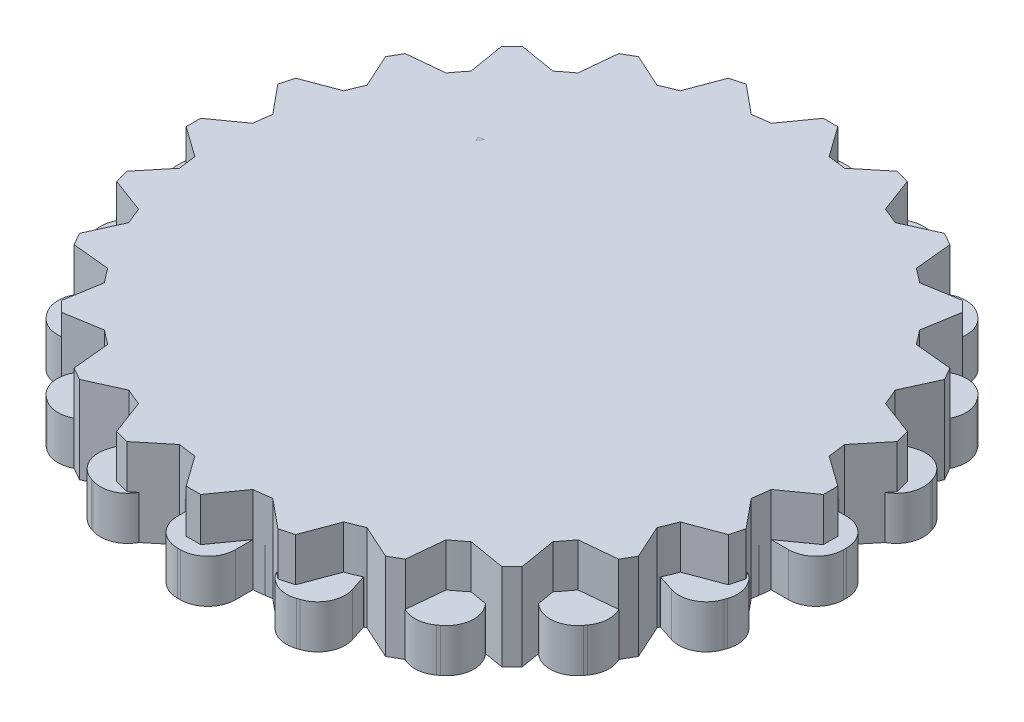
SolidWorks part; units mm, degrees
ref_plane "Front Plane" through (0, 0, 0) normal (0, 0, 1) x (1, 0, 0)
ref_plane "Top Plane" through (0, 0, 0) normal (0, 1, 0) x (1, 0, 0)
ref_plane "Right Plane" through (0, 0, 0) normal (1, 0, 0) x (0, 0, -1)
sketch "Sketch1" plane through (0, 0, 0) normal (0, 1, 0) x (1, 0, 0)
  line L86 (-3.1424, 4.8669) -> (1.8576, 4.8669)
  line L87 (-3.1424, 4.8669) -> (-3.1424, 1.8669)
  line L111 (-1.1424, 15.3669) -> (-0.1424, 15.3669)
  line L112 (-0.1424, 15.3669) -> (1.3576, 13.1649)
  line L113 (-1.1424, 15.3669) -> (-2.6424, 13.1649)
  line L114 (5.7906, 13.5092) -> (5.9886, 10.8522)
  line L115 (4.9246, 14.0092) -> (5.7906, 13.5092)
  line L116 (4.9246, 14.0092) -> (2.5245, 12.8522)
  line L117 (9.9999, 8.9339) -> (8.8429, 6.5338)
  line L118 (9.4999, 9.7999) -> (9.9999, 8.9339)
  line L119 (9.4999, 9.7999) -> (6.8429, 9.9979)
  line L120 (11.3576, 2.8669) -> (9.1556, 1.3669)
  line L121 (11.3576, 3.8669) -> (11.3576, 2.8669)
  line L122 (11.3576, 3.8669) -> (9.1556, 5.3669)
  line L123 (9.4999, -3.0661) -> (6.8429, -3.2641)
  line L124 (9.9999, -2.2001) -> (9.4999, -3.0661)
  line L125 (9.9999, -2.2001) -> (8.8429, 0.2)
  line L126 (4.9246, -7.2754) -> (2.5245, -6.1184)
  line L127 (5.7906, -6.7754) -> (4.9246, -7.2754)
  line L128 (5.7906, -6.7754) -> (5.9886, -4.1184)
  line L129 (-1.1424, -8.6331) -> (-2.6424, -6.4311)
  line L130 (-0.1424, -8.6331) -> (-1.1424, -8.6331)
  line L131 (-0.1424, -8.6331) -> (1.3576, -6.4311)
  line L132 (-7.0754, -6.7754) -> (-7.2734, -4.1184)
  line L133 (-6.2094, -7.2754) -> (-7.0754, -6.7754)
  line L134 (-6.2094, -7.2754) -> (-3.8093, -6.1184)
  line L135 (-11.2847, -2.2001) -> (-10.1277, 0.2)
  line L136 (-10.7847, -3.0661) -> (-11.2847, -2.2001)
  line L137 (-10.7847, -3.0661) -> (-8.1277, -3.2641)
  line L138 (-12.6424, 3.8669) -> (-10.4404, 5.3669)
  line L139 (-12.6424, 2.8669) -> (-12.6424, 3.8669)
  line L140 (-12.6424, 2.8669) -> (-10.4404, 1.3669)
  line L141 (-10.7847, 9.7999) -> (-8.1277, 9.9979)
  line L142 (-11.2847, 8.9339) -> (-10.7847, 9.7999)
  line L143 (-11.2847, 8.9339) -> (-10.1277, 6.5338)
  line L144 (-6.2094, 14.0092) -> (-3.8093, 12.8522)
  line L145 (-7.0754, 13.5092) -> (-6.2094, 14.0092)
  line L146 (-7.0754, 13.5092) -> (-7.2734, 10.8522)
  line L147 (-3.1424, 1.8669) -> (1.8576, 1.8669)
  line L148 (1.8576, 4.8669) -> (1.8576, 1.8669)
  line L149 (-3.1424, 4.8669) -> (1.8576, 1.8669) construction
  line L150 (-3.1424, 1.8669) -> (1.8576, 4.8669) construction
  arc A43 (-2.6424, 13.1649) -> (-3.8093, 12.8522) centre (-0.6424, 3.3669) ccw
  arc A44 (-7.2734, 10.8522) -> (-8.1277, 9.9979) centre (-0.6424, 3.3669) ccw
  arc A45 (-10.1277, 6.5338) -> (-10.4404, 5.3669) centre (-0.6424, 3.3669) ccw
  arc A46 (-10.4404, 1.3669) -> (-10.1277, 0.2) centre (-0.6424, 3.3669) ccw
  arc A47 (-8.1277, -3.2641) -> (-7.2734, -4.1184) centre (-0.6424, 3.3669) ccw
  arc A48 (-3.8093, -6.1184) -> (-2.6424, -6.4311) centre (-0.6424, 3.3669) ccw
  arc A49 (1.3576, -6.4311) -> (2.5245, -6.1184) centre (-0.6424, 3.3669) ccw
  arc A50 (5.9886, -4.1184) -> (6.8429, -3.2641) centre (-0.6424, 3.3669) ccw
  arc A51 (8.8429, 0.2) -> (9.1556, 1.3669) centre (-0.6424, 3.3669) ccw
  arc A52 (9.1556, 5.3669) -> (8.8429, 6.5338) centre (-0.6424, 3.3669) ccw
  arc A53 (6.8429, 9.9979) -> (5.9886, 10.8522) centre (-0.6424, 3.3669) ccw
  arc A54 (2.5245, 12.8522) -> (1.3576, 13.1649) centre (-0.6424, 3.3669) ccw
  point P6 (0, 0)
  point P8 (0, 0)
  point P9 (0, 0)
  point P12 (0, 2.7462)
  point P17 (0, 0)
  point P18 (0, 2.7462)
  point P22 (-2.5, 0.7462)
  point P63 (0, 0)
  point P68 (0, 0)
  point P69 (-0.6424, 3.3669)
  point P119 (0, 0)
  dimension "D1" = 20
  dimension "D2" = 3
  dimension "D3" = 5
  dimension "D8" = 12
sketch "Sketch2" plane through (0, 0, 0) normal (0, 1, 0) x (1, 0, 0)
  line L0 (-2, 0) -> (2, 0)
  line L1 (-23, -0.1) -> (-23, 0.1)
  line L2 (-21.1, 2) -> (-19.8997, 2)
  line L3 (-21.1, -2) -> (-19.8997, -2)
  line L4 (-20.6853, 4.6181) -> (-19.5438, 4.2472)
  line L5 (-19.4493, 8.4224) -> (-18.3078, 8.0515)
  line L6 (-21.9052, 7.0123) -> (-21.8434, 7.2025)
  line L7 (-18.2458, 10.7842) -> (-17.2748, 10.0787)
  line L8 (-15.8947, 14.0203) -> (-14.9237, 13.3148)
  line L9 (-18.6662, 13.4382) -> (-18.5486, 13.6)
  line L10 (-14.0203, 15.8947) -> (-13.3148, 14.9237)
  line L11 (-10.7842, 18.2458) -> (-10.0787, 17.2748)
  line L12 (-13.6, 18.5486) -> (-13.4382, 18.6662)
  line L13 (-8.4224, 19.4493) -> (-8.0515, 18.3078)
  line L14 (-4.6181, 20.6853) -> (-4.2472, 19.5438)
  line L15 (-7.2025, 21.8434) -> (-7.0123, 21.9052)
  line L16 (-2, 21.1) -> (-2, 19.8997)
  line L17 (2, 21.1) -> (2, 19.8997)
  line L18 (-0.1, 23) -> (0.1, 23)
  line L19 (4.6181, 20.6853) -> (4.2472, 19.5438)
  line L20 (8.4224, 19.4493) -> (8.0515, 18.3078)
  line L21 (7.0123, 21.9052) -> (7.2025, 21.8434)
  line L22 (10.7842, 18.2458) -> (10.0787, 17.2748)
  line L23 (14.0203, 15.8947) -> (13.3148, 14.9237)
  line L24 (13.4382, 18.6662) -> (13.6, 18.5486)
  line L25 (15.8947, 14.0203) -> (14.9237, 13.3148)
  line L26 (18.2458, 10.7842) -> (17.2748, 10.0787)
  line L27 (18.5486, 13.6) -> (18.6662, 13.4382)
  line L28 (19.4493, 8.4224) -> (18.3078, 8.0515)
  line L29 (20.6853, 4.6181) -> (19.5438, 4.2472)
  line L30 (21.8434, 7.2025) -> (21.9052, 7.0123)
  line L31 (21.1, 2) -> (19.8997, 2)
  line L32 (21.1, -2) -> (19.8997, -2)
  line L33 (23, 0.1) -> (23, -0.1)
  line L34 (20.6853, -4.6181) -> (19.5438, -4.2472)
  line L35 (19.4493, -8.4224) -> (18.3078, -8.0515)
  line L36 (21.9052, -7.0123) -> (21.8434, -7.2025)
  line L37 (18.2458, -10.7842) -> (17.2748, -10.0787)
  line L38 (15.8947, -14.0203) -> (14.9237, -13.3148)
  line L39 (18.6662, -13.4382) -> (18.5486, -13.6)
  line L40 (14.0203, -15.8947) -> (13.3148, -14.9237)
  line L41 (10.7842, -18.2458) -> (10.0787, -17.2748)
  line L42 (13.6, -18.5486) -> (13.4382, -18.6662)
  line L43 (8.4224, -19.4493) -> (8.0515, -18.3078)
  line L44 (4.6181, -20.6853) -> (4.2472, -19.5438)
  line L45 (7.2025, -21.8434) -> (7.0123, -21.9052)
  line L46 (2, -21.1) -> (2, -19.8997)
  line L47 (-2, -21.1) -> (-2, -19.8997)
  line L48 (0.1, -23) -> (-0.1, -23)
  line L49 (-4.6181, -20.6853) -> (-4.2472, -19.5438)
  line L50 (-8.4224, -19.4493) -> (-8.0515, -18.3078)
  line L51 (-7.0123, -21.9052) -> (-7.2025, -21.8434)
  line L52 (-10.7842, -18.2458) -> (-10.0787, -17.2748)
  line L53 (-14.0203, -15.8947) -> (-13.3148, -14.9237)
  line L54 (-13.4382, -18.6662) -> (-13.6, -18.5486)
  line L55 (-15.8947, -14.0203) -> (-14.9237, -13.3148)
  line L56 (-18.2458, -10.7842) -> (-17.2748, -10.0787)
  line L57 (-18.5486, -13.6) -> (-18.6662, -13.4382)
  line L58 (-19.4493, -8.4224) -> (-18.3078, -8.0515)
  line L59 (-20.6853, -4.6181) -> (-19.5438, -4.2472)
  line L60 (-21.8434, -7.2025) -> (-21.9052, -7.0123)
  arc A0 (-18.3078, -8.0515) -> (-17.2748, -10.0787) centre (0, 0) ccw
  arc A1 (-21.1, 2) -> (-23, 0.1) centre (-21.1, 0.1) ccw
  arc A2 (-21.1, -2) -> (-23, -0.1) centre (-21.1, -0.1) cw
  arc A3 (-20.6853, 4.6181) -> (-21.9052, 7.0123) centre (-20.0982, 6.4252) cw
  arc A4 (-19.4493, 8.4224) -> (-21.8434, 7.2025) centre (-20.0364, 6.6154) ccw
  arc A5 (-18.2458, 10.7842) -> (-18.6662, 13.4382) centre (-17.129, 12.3214) cw
  arc A6 (-15.8947, 14.0203) -> (-18.5486, 13.6) centre (-17.0115, 12.4832) ccw
  arc A7 (-14.0203, 15.8947) -> (-13.6, 18.5486) centre (-12.4832, 17.0115) cw
  arc A8 (-10.7842, 18.2458) -> (-13.4382, 18.6662) centre (-12.3214, 17.129) ccw
  arc A9 (-8.4224, 19.4493) -> (-7.2025, 21.8434) centre (-6.6154, 20.0364) cw
  arc A10 (-4.6181, 20.6853) -> (-7.0123, 21.9052) centre (-6.4252, 20.0982) ccw
  arc A11 (-2, 21.1) -> (-0.1, 23) centre (-0.1, 21.1) cw
  arc A12 (2, 21.1) -> (0.1, 23) centre (0.1, 21.1) ccw
  arc A13 (4.6181, 20.6853) -> (7.0123, 21.9052) centre (6.4252, 20.0982) cw
  arc A14 (8.4224, 19.4493) -> (7.2025, 21.8434) centre (6.6154, 20.0364) ccw
  arc A15 (10.7842, 18.2458) -> (13.4382, 18.6662) centre (12.3214, 17.129) cw
  arc A16 (14.0203, 15.8947) -> (13.6, 18.5486) centre (12.4832, 17.0115) ccw
  arc A17 (15.8947, 14.0203) -> (18.5486, 13.6) centre (17.0115, 12.4832) cw
  arc A18 (18.2458, 10.7842) -> (18.6662, 13.4382) centre (17.129, 12.3214) ccw
  arc A19 (19.4493, 8.4224) -> (21.8434, 7.2025) centre (20.0364, 6.6154) cw
  arc A20 (20.6853, 4.6181) -> (21.9052, 7.0123) centre (20.0982, 6.4252) ccw
  arc A21 (21.1, 2) -> (23, 0.1) centre (21.1, 0.1) cw
  arc A22 (21.1, -2) -> (23, -0.1) centre (21.1, -0.1) ccw
  arc A23 (20.6853, -4.6181) -> (21.9052, -7.0123) centre (20.0982, -6.4252) cw
  arc A24 (19.4493, -8.4224) -> (21.8434, -7.2025) centre (20.0364, -6.6154) ccw
  arc A25 (18.2458, -10.7842) -> (18.6662, -13.4382) centre (17.129, -12.3214) cw
  arc A26 (15.8947, -14.0203) -> (18.5486, -13.6) centre (17.0115, -12.4832) ccw
  arc A27 (14.0203, -15.8947) -> (13.6, -18.5486) centre (12.4832, -17.0115) cw
  arc A28 (10.7842, -18.2458) -> (13.4382, -18.6662) centre (12.3214, -17.129) ccw
  arc A29 (8.4224, -19.4493) -> (7.2025, -21.8434) centre (6.6154, -20.0364) cw
  arc A30 (4.6181, -20.6853) -> (7.0123, -21.9052) centre (6.4252, -20.0982) ccw
  arc A31 (2, -21.1) -> (0.1, -23) centre (0.1, -21.1) cw
  arc A32 (-2, -21.1) -> (-0.1, -23) centre (-0.1, -21.1) ccw
  arc A33 (-4.6181, -20.6853) -> (-7.0123, -21.9052) centre (-6.4252, -20.0982) cw
  arc A34 (-8.4224, -19.4493) -> (-7.2025, -21.8434) centre (-6.6154, -20.0364) ccw
  arc A35 (-10.7842, -18.2458) -> (-13.4382, -18.6662) centre (-12.3214, -17.129) cw
  arc A36 (-14.0203, -15.8947) -> (-13.6, -18.5486) centre (-12.4832, -17.0115) ccw
  arc A37 (-15.8947, -14.0203) -> (-18.5486, -13.6) centre (-17.0115, -12.4832) cw
  arc A38 (-18.2458, -10.7842) -> (-18.6662, -13.4382) centre (-17.129, -12.3214) ccw
  arc A39 (-19.4493, -8.4224) -> (-21.8434, -7.2025) centre (-20.0364, -6.6154) cw
  arc A40 (-20.6853, -4.6181) -> (-21.9052, -7.0123) centre (-20.0982, -6.4252) ccw
  arc A41 (-19.8997, -2) -> (-19.5438, -4.2472) centre (0, 0) ccw
  arc A42 (-19.5438, 4.2472) -> (-19.8997, 2) centre (0, 0) ccw
  arc A43 (-17.2748, 10.0787) -> (-18.3078, 8.0515) centre (0, 0) ccw
  arc A44 (-13.3148, 14.9237) -> (-14.9237, 13.3148) centre (0, 0) ccw
  arc A45 (-8.0515, 18.3078) -> (-10.0787, 17.2748) centre (0, 0) ccw
  arc A46 (-2, 19.8997) -> (-4.2472, 19.5438) centre (0, 0) ccw
  arc A47 (4.2472, 19.5438) -> (2, 19.8997) centre (0, 0) ccw
  arc A48 (10.0787, 17.2748) -> (8.0515, 18.3078) centre (0, 0) ccw
  arc A49 (14.9237, 13.3148) -> (13.3148, 14.9237) centre (0, 0) ccw
  arc A50 (18.3078, 8.0515) -> (17.2748, 10.0787) centre (0, 0) ccw
  arc A51 (19.8997, 2) -> (19.5438, 4.2472) centre (0, 0) ccw
  arc A52 (19.5438, -4.2472) -> (19.8997, -2) centre (0, 0) ccw
  arc A53 (17.2748, -10.0787) -> (18.3078, -8.0515) centre (0, 0) ccw
  arc A54 (13.3148, -14.9237) -> (14.9237, -13.3148) centre (0, 0) ccw
  arc A55 (8.0515, -18.3078) -> (10.0787, -17.2748) centre (0, 0) ccw
  arc A56 (2, -19.8997) -> (4.2472, -19.5438) centre (0, 0) ccw
  arc A57 (-10.0787, -17.2748) -> (-8.0515, -18.3078) centre (0, 0) ccw
  arc A58 (-4.2472, -19.5438) -> (-2, -19.8997) centre (0, 0) ccw
  arc A59 (-14.9237, -13.3148) -> (-13.3148, -14.9237) centre (0, 0) ccw
  point P6 (0, 0)
  point P10 (-23, 2)
  point P170 (0, 0)
  dimension "D1" = 40
  dimension "D4" = 1.9
  dimension "D5" = 20
extrude "Boss-Extrude3" add sketch "Sketch2" along normal blind 3
sketch "Sketch3" plane through (0, 0, 0) normal (0, 1, 0) x (1, 0, 0)
  line L0 (-22, 0) -> (22, 0)
  line L1 (22, -0.5) -> (22, 0.5)
  line L2 (22, 0.5) -> (19.8997, 2)
  line L3 (22, -0.5) -> (19.8997, -2)
  line L4 (21.3798, -5.2111) -> (19.7393, -3.2186)
  line L5 (21.121, -6.177) -> (21.3798, -5.2111)
  line L6 (21.121, -6.177) -> (18.704, -7.0823)
  line L7 (19.3026, -10.567) -> (18.2337, -8.2178)
  line L8 (18.8026, -11.433) -> (19.3026, -10.567)
  line L9 (18.8026, -11.433) -> (16.2337, -11.6819)
  line L10 (15.9099, -15.2028) -> (15.4855, -12.657)
  line L11 (15.2028, -15.9099) -> (15.9099, -15.2028)
  line L12 (15.2028, -15.9099) -> (12.657, -15.4855)
  line L13 (11.433, -18.8026) -> (11.6819, -16.2337)
  line L14 (10.567, -19.3026) -> (11.433, -18.8026)
  line L15 (10.567, -19.3026) -> (8.2178, -18.2337)
  line L16 (6.177, -21.121) -> (7.0823, -18.704)
  line L17 (5.2111, -21.3798) -> (6.177, -21.121)
  line L18 (5.2111, -21.3798) -> (3.2186, -19.7393)
  line L19 (0.5, -22) -> (2, -19.8997)
  line L20 (-0.5, -22) -> (0.5, -22)
  line L21 (-0.5, -22) -> (-2, -19.8997)
  line L22 (-5.2111, -21.3798) -> (-3.2186, -19.7393)
  line L23 (-6.177, -21.121) -> (-5.2111, -21.3798)
  line L24 (-6.177, -21.121) -> (-7.0823, -18.704)
  line L25 (-10.567, -19.3026) -> (-8.2178, -18.2337)
  line L26 (-11.433, -18.8026) -> (-10.567, -19.3026)
  line L27 (-11.433, -18.8026) -> (-11.6819, -16.2337)
  line L28 (-15.2028, -15.9099) -> (-12.657, -15.4855)
  line L29 (-15.9099, -15.2028) -> (-15.2028, -15.9099)
  line L30 (-15.9099, -15.2028) -> (-15.4855, -12.657)
  line L31 (-18.8026, -11.433) -> (-16.2337, -11.6819)
  line L32 (-19.3026, -10.567) -> (-18.8026, -11.433)
  line L33 (-19.3026, -10.567) -> (-18.2337, -8.2178)
  line L34 (-21.121, -6.177) -> (-18.704, -7.0823)
  line L35 (-21.3798, -5.2111) -> (-21.121, -6.177)
  line L36 (-21.3798, -5.2111) -> (-19.7393, -3.2186)
  line L37 (-22, -0.5) -> (-19.8997, -2)
  line L38 (-22, 0.5) -> (-22, -0.5)
  line L39 (-22, 0.5) -> (-19.8997, 2)
  line L40 (-21.3798, 5.2111) -> (-19.7393, 3.2186)
  line L41 (-21.121, 6.177) -> (-21.3798, 5.2111)
  line L42 (-21.121, 6.177) -> (-18.704, 7.0823)
  line L43 (-19.3026, 10.567) -> (-18.2337, 8.2178)
  line L44 (-18.8026, 11.433) -> (-19.3026, 10.567)
  line L45 (-18.8026, 11.433) -> (-16.2337, 11.6819)
  line L46 (-15.9099, 15.2028) -> (-15.4855, 12.657)
  line L47 (-15.2028, 15.9099) -> (-15.9099, 15.2028)
  line L48 (-15.2028, 15.9099) -> (-12.657, 15.4855)
  line L49 (-11.433, 18.8026) -> (-11.6819, 16.2337)
  line L50 (-10.567, 19.3026) -> (-11.433, 18.8026)
  line L51 (-10.567, 19.3026) -> (-8.2178, 18.2337)
  line L52 (-6.177, 21.121) -> (-7.0823, 18.704)
  line L53 (-5.2111, 21.3798) -> (-6.177, 21.121)
  line L54 (-5.2111, 21.3798) -> (-3.2186, 19.7393)
  line L55 (-0.5, 22) -> (-2, 19.8997)
  line L56 (0.5, 22) -> (-0.5, 22)
  line L57 (0.5, 22) -> (2, 19.8997)
  line L58 (5.2111, 21.3798) -> (3.2186, 19.7393)
  line L59 (6.177, 21.121) -> (5.2111, 21.3798)
  line L60 (6.177, 21.121) -> (7.0823, 18.704)
  line L61 (10.567, 19.3026) -> (8.2178, 18.2337)
  line L62 (11.433, 18.8026) -> (10.567, 19.3026)
  line L63 (11.433, 18.8026) -> (11.6819, 16.2337)
  line L64 (15.2028, 15.9099) -> (12.657, 15.4855)
  line L65 (15.9099, 15.2028) -> (15.2028, 15.9099)
  line L66 (15.9099, 15.2028) -> (15.4855, 12.657)
  line L67 (18.8026, 11.433) -> (16.2337, 11.6819)
  line L68 (19.3026, 10.567) -> (18.8026, 11.433)
  line L69 (19.3026, 10.567) -> (18.2337, 8.2178)
  line L70 (21.121, 6.177) -> (18.704, 7.0823)
  line L71 (21.3798, 5.2111) -> (21.121, 6.177)
  line L72 (21.3798, 5.2111) -> (19.7393, 3.2186)
  arc A0 (-8.2178, -18.2337) -> (-7.0823, -18.704) centre (0, 0) ccw
  arc A1 (-12.657, -15.4855) -> (-11.6819, -16.2337) centre (0, 0) ccw
  arc A2 (-16.2337, -11.6819) -> (-15.4855, -12.657) centre (0, 0) ccw
  arc A3 (-18.704, -7.0823) -> (-18.2337, -8.2178) centre (0, 0) ccw
  arc A4 (-19.8997, -2) -> (-19.7393, -3.2186) centre (0, 0) ccw
  arc A5 (-19.7393, 3.2186) -> (-19.8997, 2) centre (0, 0) ccw
  arc A6 (-18.2337, 8.2178) -> (-18.704, 7.0823) centre (0, 0) ccw
  arc A7 (-15.4855, 12.657) -> (-16.2337, 11.6819) centre (0, 0) ccw
  arc A8 (-11.6819, 16.2337) -> (-12.657, 15.4855) centre (0, 0) ccw
  arc A9 (-7.0823, 18.704) -> (-8.2178, 18.2337) centre (0, 0) ccw
  arc A10 (-2, 19.8997) -> (-3.2186, 19.7393) centre (0, 0) ccw
  arc A11 (3.2186, 19.7393) -> (2, 19.8997) centre (0, 0) ccw
  arc A12 (8.2178, 18.2337) -> (7.0823, 18.704) centre (0, 0) ccw
  arc A13 (12.657, 15.4855) -> (11.6819, 16.2337) centre (0, 0) ccw
  arc A14 (16.2337, 11.6819) -> (15.4855, 12.657) centre (0, 0) ccw
  arc A15 (18.704, 7.0823) -> (18.2337, 8.2178) centre (0, 0) ccw
  arc A16 (19.8997, 2) -> (19.7393, 3.2186) centre (0, 0) ccw
  arc A17 (19.7393, -3.2186) -> (19.8997, -2) centre (0, 0) ccw
  arc A18 (18.2337, -8.2178) -> (18.704, -7.0823) centre (0, 0) ccw
  arc A19 (-3.2186, -19.7393) -> (-2, -19.8997) centre (0, 0) ccw
  arc A20 (2, -19.8997) -> (3.2186, -19.7393) centre (0, 0) ccw
  arc A21 (7.0823, -18.704) -> (8.2178, -18.2337) centre (0, 0) ccw
  arc A22 (11.6819, -16.2337) -> (12.657, -15.4855) centre (0, 0) ccw
  arc A23 (15.4855, -12.657) -> (16.2337, -11.6819) centre (0, 0) ccw
  point P6 (0, 0)
  point P7 (0, -12.952)
  point P8 (-6.2727, 0)
  point P9 (11.4668, 0)
  point P10 (0, 0)
  point P108 (0, 0)
  dimension "D1" = 40
  dimension "D2" = 22
  dimension "D3" = 2
  dimension "D4" = 24
extrude "Boss-Extrude5" add sketch "Sketch3" along normal blind 6 separate body contours L2 A16 L72 L71 L70 A15 L69 L68 L67 A14 L66 L65 L64 A13 L63 L62 L61 A12 L60 L59 L58 A11 L57 L56 L55 A10 L54 L53 L52 A9 L51 L50 L49 A8 L48 L47 L46 A7 L45 L44 L43 A6 L42 L41 L40 A5 L39 L38 L0 L1 | L10 A23 L9 L8 L7 A18 L6 L5 L4 A17 L3 L1 L0 L38 L37 A4 L36 L35 L34 A3 L33 L32 L31 A2 L30 L29 L28 A1 L27 L26 L25 A0 L24 L23 L22 A19 L21 L20 L19 A20 L18 L17 L16 A21 L15 L14 L13 A22 L12 L11
extrude "Boss-Extrude6" add sketch "Sketch1" along normal blind 6 separate body
sketch "Sketch5" plane through (0, 6, 0) normal (0, 1, 0) x (1, 0, 0)
  line L0 (-0.6424, 15.3669) -> (-0.6424, -8.6331) construction
  line L1 (-0.1424, 15.3669) -> (-1.1424, 15.3669) construction
  line L2 (-1.1424, -8.6331) -> (-0.1424, -8.6331) construction
  line L3 (11.3576, 3.3669) -> (-12.6424, 3.3669) construction
  line L4 (11.3576, 2.8669) -> (11.3576, 3.8669) construction
  line L5 (-12.6424, 3.8669) -> (-12.6424, 2.8669) construction
  circle A0 centre (-0.6424, 3.3669) radius 5.1751
